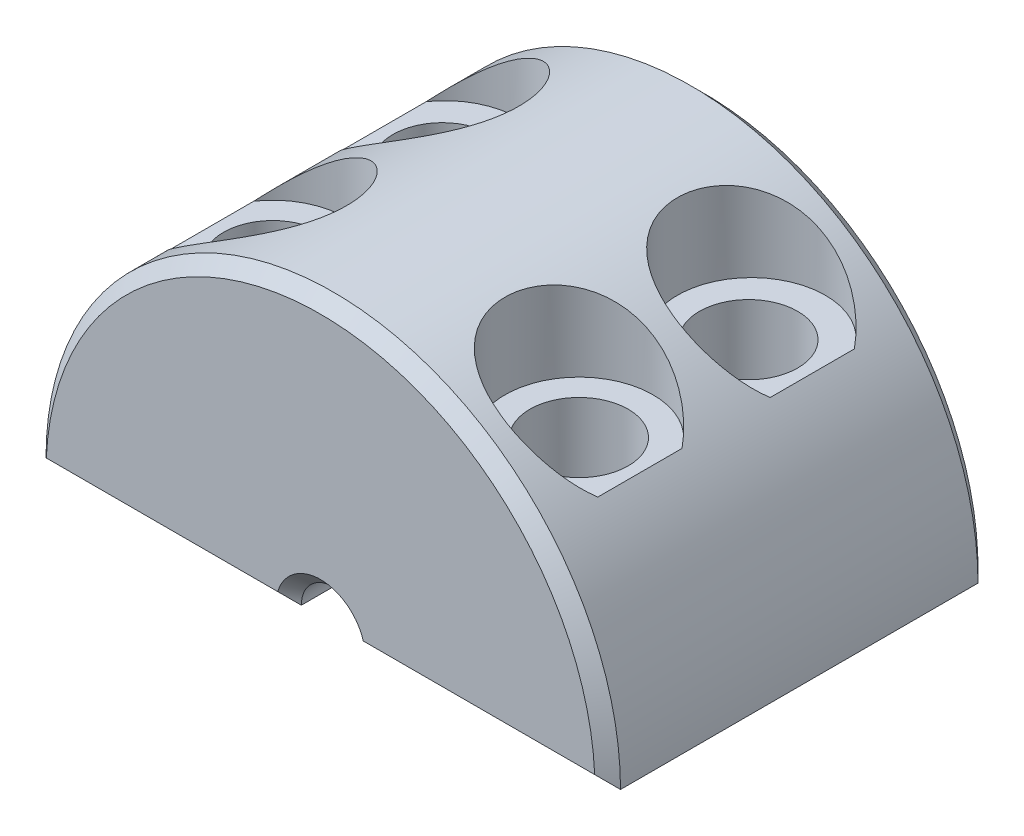
SolidWorks part; units mm, degrees
ref_plane "Front Plane" through (0, 0, 0) normal (0, 0, 1) x (1, 0, 0)
ref_plane "Top Plane" through (0, 0, 0) normal (0, 1, 0) x (1, 0, 0)
ref_plane "Right Plane" through (0, 0, 0) normal (1, 0, 0) x (0, 0, -1)
sketch "Sketch2" plane through (0, 0, 0) normal (0, 0, 1) x (1, 0, 0)
  line L0 (-11.43, 0) -> (-1.27, 0)
  line L1 (1.27, 0) -> (11.43, 0)
  arc A0 (11.43, 0) -> (-11.43, 0) centre (0, 0) ccw
  arc A1 (1.27, 0) -> (-1.27, 0) centre (0, 0) ccw
  point P7 (0, 0)
  dimension "D1" = 22.86
  dimension "D2" = 2.54
extrude "Boss-Extrude2" add sketch "Sketch2" along normal blind 15.24
chamfer "Chamfer1" distance 0.508 angle 45 8 edges at (-6.35, 0, 15.24) (0, 11.43, 15.24) (6.35, 0, 15.24) (0, 1.27, 15.24) (6.35, 0, 0) (0, 11.43, 0) (-6.35, 0, 0) (0, 1.27, 0)
ref_plane "Plane1" through (0, 11.43, 0) normal (0, 1, 0) x (1, 0, 0)
sketch "Sketch3" plane through (0, 11.43, 0) normal (0, 1, 0) x (1, 0, 0)
  line L0 (0, 0) -> (0, -15.3522)
sketch "Sketch4" plane through (0, 11.43, 0) normal (0, 1, 0) x (1, 0, 0)
  line L0 (0, 0) -> (0, -15.3522) construction
  line L1 (-11.43, -14.732) -> (11.43, -14.732) construction
  line L2 (0, -15.3522) -> (0, 0)
  line L3 (10.4007, -7.6761) -> (-10.4007, -7.6761)
  line L4 (11.43, -0.508) -> (-11.43, -0.508) construction
  circle A0 centre (-6.096, -4.191) radius 2.9464
  circle A1 centre (-6.096, -11.049) radius 2.9464
  circle A2 centre (6.096, -4.191) radius 2.9464
  circle A3 centre (6.096, -11.049) radius 2.9464
  circle A4 centre (-6.096, -11.049) radius 1.9558
  circle A5 centre (-6.096, -4.3032) radius 1.9558
  circle A6 centre (6.096, -11.049) radius 1.9558
  circle A7 centre (6.096, -4.3032) radius 1.9558
  point P18 (0, 0)
  point P21 (0, -7.6761)
  dimension "D1" = 5.8928
  dimension "D4" = 5.8928
  dimension "D7" = 3.9116
  dimension "D2" = 3.683
  dimension "D3" = 6.096
  dimension "D5" = 6.096
  dimension "D6" = 3.683
sketch "Sketch5" plane through (0, 11.43, 0) normal (0, 1, 0) x (1, 0, 0)
  line L0 (0, -7.6761) -> (12.7133, -7.6761) construction
  line L1 (0, 0) -> (0, -15.3522) construction
  line L2 (12.7133, -7.6761) -> (-11.43, -7.62) construction
  line L3 (-11.43, -14.732) -> (-11.43, -0.508) construction
extrude "Cut-Extrude1" cut sketch "Sketch4" against normal blind 3.81 contours A5 | A7 | A6 | A4 | A1 | A0 | A3 | A2
sketch "Sketch6" plane through (0, 11.43, 0) normal (0, 1, 0) x (1, 0, 0)
  line L0 (-12.7133, -7.6761) -> (12.7133, -7.6761)
  line L2 (0, -7.6761) -> (0, -15.3522)
  line L3 (0, -15.3522) -> (0, 0)
  circle A0 centre (-6.096, -4.3032) radius 1.9558
  circle A1 centre (-6.096, -11.049) radius 1.9558
  circle A2 centre (6.096, -11.049) radius 1.9558
  circle A3 centre (6.096, -4.3032) radius 1.9558
  point P7 (0, -7.6761)
  dimension "D1" = 3.9116
extrude "Cut-Extrude2" cut sketch "Sketch6" against normal through all contours A0 | A1 | A2 | A3
